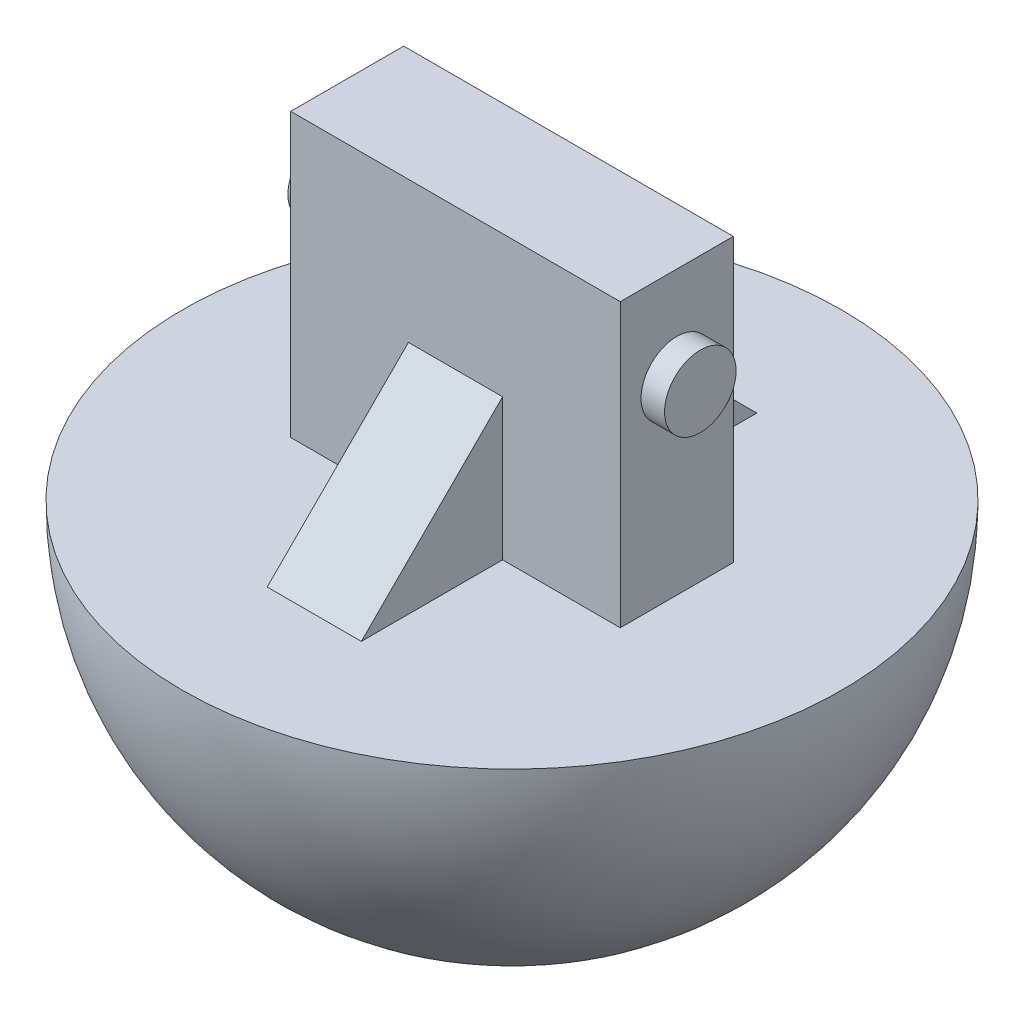
SolidWorks part; units mm, degrees
ref_plane "Front Plane" through (0, 0, 0) normal (0, 0, 1) x (1, 0, 0)
ref_plane "Top Plane" through (0, 0, 0) normal (0, 1, 0) x (1, 0, 0)
ref_plane "Right Plane" through (0, 0, 0) normal (1, 0, 0) x (0, 0, -1)
sketch "Sketch1" plane through (0, 0, 0) normal (0, 0, 1) x (1, 0, 0)
  line L1 (22.225, 19.05) -> (-22.225, 19.05)
  line L2 (22.225, 19.05) -> (22.225, -19.05)
  line L3 (22.225, -19.05) -> (-22.225, -19.05)
  line L4 (-22.225, 19.05) -> (-22.225, -19.05)
  line L5 (22.225, 19.05) -> (-22.225, -19.05) construction
  line L6 (22.225, -19.05) -> (-22.225, 19.05) construction
  point P0 (0, 0)
  dimension "D1" = 44.45
  dimension "D2" = 38.1
extrude "Boss-Extrude1" add sketch "Sketch1" along normal blind 15.24
sketch "Sketch2" plane through (22.225, 0, 0) normal (1, 0, 0) x (0, 0, -1)
  line L0 (-7.62, -19.05) -> (-7.62, 19.05) construction
  line L1 (-15.24, -19.05) -> (0, -19.05) construction
  line L2 (-15.24, 19.05) -> (0, 19.05) construction
  circle A0 centre (-7.62, 6.35) radius 4.826
  point P8 (0, 0)
  dimension "D1" = 9.652
  dimension "D2" = 12.7
extrude "Boss-Extrude2" add sketch "Sketch2" along normal blind 3.175
mirror "Mirror1" about plane through (0, 0, 0) normal (1, 0, 0) of "Boss-Extrude2"
sketch "Sketch5" plane through (0, 0, 0) normal (1, 0, 0) x (0, 0, -1)
  line L0 (-52.07, -19.05) -> (-7.62, -19.05)
  line L1 (-15.24, -19.05) -> (0, -19.05) construction
  line L2 (-7.62, -19.05) -> (-7.62, -63.5)
  arc A0 (-7.62, -63.5) -> (-52.07, -19.05) centre (-7.62, -19.05) cw
  dimension "D1" = 44.45
revolve "Revolve1" add sketch "Sketch5" angle 360 about L2
sketch "Sketch7" plane through (0, 0, 0) normal (1, 0, 0) x (0, 0, -1)
  line L0 (-15.24, 0) -> (-15.24, -19.05)
  line L1 (-15.24, -19.05) -> (-15.24, 19.05) construction
  line L2 (36.83, -19.05) -> (-52.07, -19.05) construction
  line L3 (-15.24, -19.05) -> (-34.29, -19.05)
  line L4 (-34.29, -19.05) -> (-15.24, 0)
  dimension "D1" = 19.05
extrude "Boss-Extrude3" add sketch "Sketch7" along normal mid plane 12.7
ref_plane "Plane1" through (0, 0, 7.62) normal (0, 0, 1) x (1, 0, 0)
mirror "Mirror3" about plane through (0, 0, 7.62) normal (0, 0, 1) of "Boss-Extrude3"
